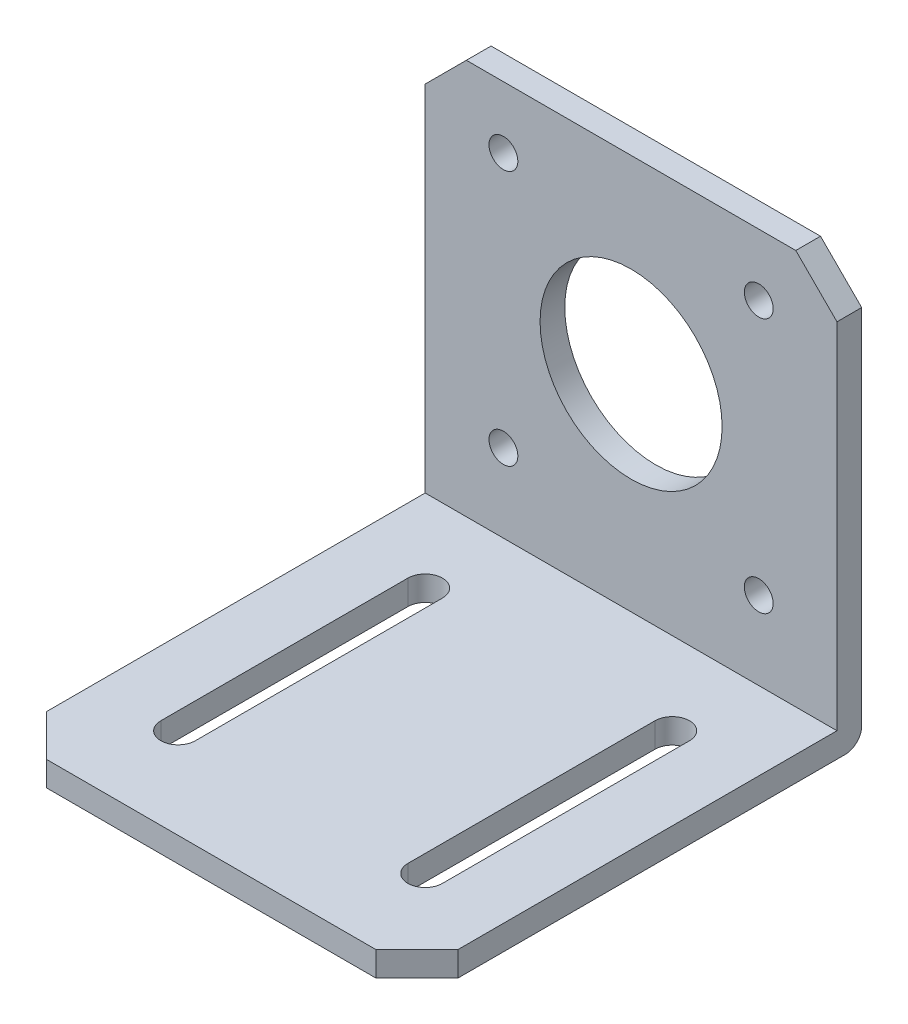
SolidWorks part; units mm, degrees
ref_plane "前视基准面" through (0, 0, 0) normal (0, 0, 1) x (1, 0, 0)
ref_plane "上视基准面" through (0, 0, 0) normal (0, 1, 0) x (1, 0, 0)
ref_plane "右视基准面" through (0, 0, 0) normal (1, 0, 0) x (0, 0, -1)
sketch "草图1" plane through (0, 0, 0) normal (0, 0, 1) x (1, 0, 0)
  line L0 (25, 29.7087) -> (25, -16.2913)
  line L1 (25, -16.2913) -> (-25, -16.2913)
  line L2 (-25, -16.2913) -> (-25, 29.7087)
  line L3 (-20, 34.7087) -> (20, 34.7087)
  line L4 (-25, 29.7087) -> (-20, 34.7087)
  line L5 (20, 34.7087) -> (25, 29.7087)
  line L6 (0, 11.7087) -> (0, 42.19) construction
  circle A0 centre (-15.5, 27.2087) radius 1.75
  circle A1 centre (15.5, 27.2087) radius 1.75
  circle A2 centre (-15.5, -3.7913) radius 1.75
  circle A3 centre (15.5, -3.7913) radius 1.75
  circle A4 centre (0, 11.7087) radius 11.05
  point P0 (25, 34.7087)
  point P3 (-25, 34.7087)
  dimension "D5" = 3.5
  dimension "D6" = 22.1
  dimension "D1" = 51
  dimension "D2" = 50
  dimension "D3" = 31
  dimension "D4" = 25
  dimension "D7" = 9.5
  dimension "D8" = 9.5
  dimension "D9" = 28
  dimension "D10" = 15.5
  dimension "D11" = 15.5
  dimension "D12" = 15.5
  dimension "D13" = 15.5
  dimension "D14" = 31
extrude "凸台-拉伸1" add sketch "草图1" along normal blind 3
sketch "草图2" plane through (0, 0, 3) normal (0, 0, 1) x (1, 0, 0)
  line L0 (-25, -13.2913) -> (25, -13.2913)
  line L1 (-25, 29.7087) -> (-25, -16.2913) construction
  line L2 (25, -16.2913) -> (25, 29.7087) construction
  line L3 (-25, -16.2913) -> (25, -16.2913) construction
  line L10 (-25, -16.2913) -> (25, -16.2913)
  line L11 (25, -16.2913) -> (25, 29.7087)
  line L12 (25, 29.7087) -> (20, 34.7087)
  line L13 (20, 34.7087) -> (-20, 34.7087)
  line L14 (-20, 34.7087) -> (-25, 29.7087)
  line L15 (-25, 29.7087) -> (-25, -16.2913)
  line L16 (-25, -16.2913) -> (25, -16.2913)
  line L17 (25, -16.2913) -> (25, -13.2913)
  line L21 (-25, -13.2913) -> (-25, -16.2913)
  dimension "D1" = 3
  dimension "D2" = 0
extrude "凸台-拉伸2" add sketch "草图2" along normal blind 51
fillet "圆角1" radius 2 1 edges at (0, -16.2913, 0)
sketch "草图3" plane through (0, -13.2913, 0) normal (0, 1, 0) x (1, 0, 0)
  line L0 (-17.1, -13) -> (-17.1, -43)
  line L1 (25, -54) -> (-25, -54) construction
  line L2 (-12.9, -43) -> (-12.9, -13)
  line L3 (12.9, -13) -> (12.9, -43)
  line L4 (17.1, -13) -> (17.1, -43)
  line L5 (25, -54) -> (25, -3) construction
  line L7 (-25, -54) -> (-25, -3) construction
  arc A0 (-12.9, -13) -> (-17.1, -13) centre (-15, -13) ccw
  arc A1 (17.1, -13) -> (12.9, -13) centre (15, -13) ccw
  arc A2 (12.9, -43) -> (17.1, -43) centre (15, -43) ccw
  arc A3 (-17.1, -43) -> (-12.9, -43) centre (-15, -43) ccw
  dimension "D1" = 4.2
  dimension "D2" = 30
  dimension "D3" = 11
  dimension "D4" = 10
  dimension "D5" = 30
  dimension "D6" = 10
extrude "切除-拉伸1" cut sketch "草图3" against normal blind 51
chamfer "倒角1" distance 5 angle 45 2 edges at (-25, -14.7913, 54) (25, -14.7913, 54)
sketch "草图4" [suppressed] plane through (25, 0, 0) normal (1, 0, 0) x (0, 0, -1)
  line L0 (-3, 6.7087) -> (-16, -13.2913)
  line L1 (-3, -13.2913) -> (-3, 29.7087) construction
  line L2 (-49, -13.2913) -> (-3, -13.2913) construction
  line L3 (-16, -13.2913) -> (-5, -13.2913)
  line L4 (-5, -13.2913) -> (-3, -10.2144)
  line L5 (-3, -10.2144) -> (-3, 6.7087)
  dimension "D1" = 20
  dimension "D2" = 13
  dimension "D3" = 2
extrude "凸台-拉伸3" [suppressed] add sketch "草图4" against normal blind 3
mirror "镜向1" [suppressed] about plane through (0, 0, 0) normal (1, 0, 0)
fillet "圆角3" [suppressed] radius 2
